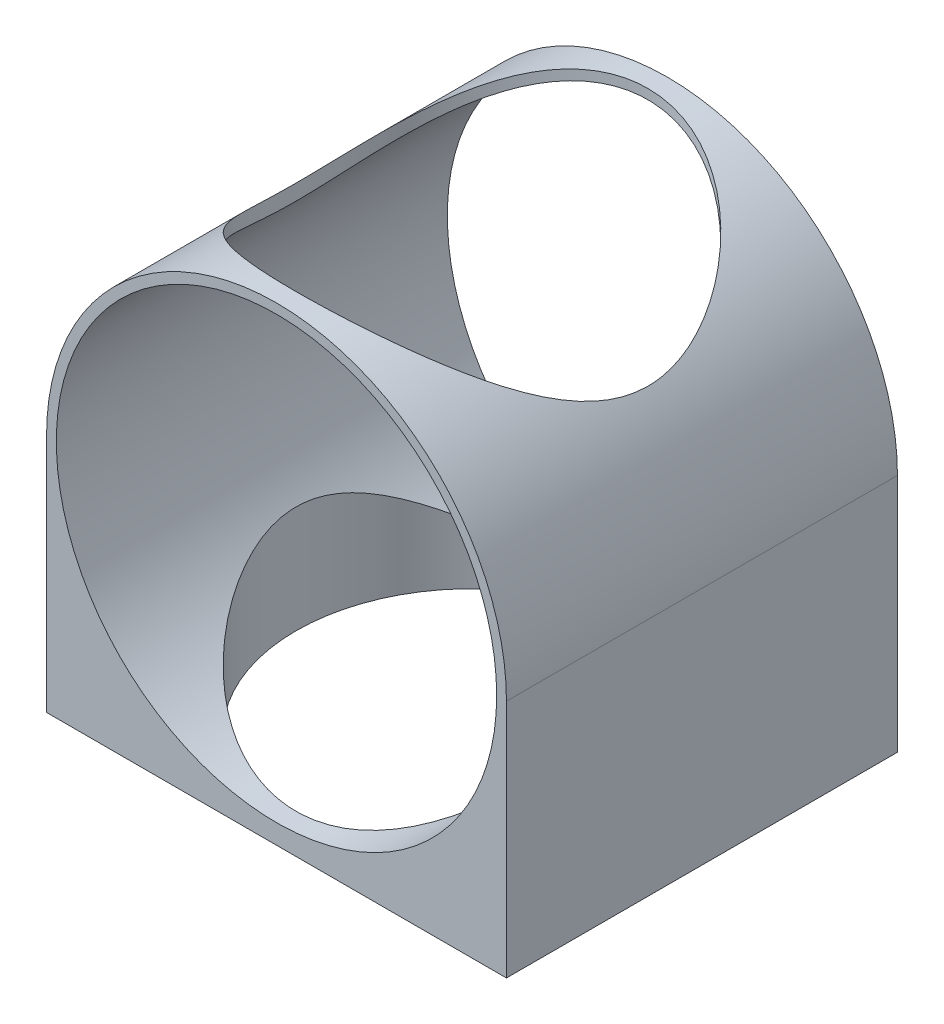
SolidWorks part; units mm, degrees
ref_plane "Front Plane" through (0, 0, 0) normal (0, 0, 1) x (1, 0, 0)
ref_plane "Top Plane" through (0, 0, 0) normal (0, 1, 0) x (1, 0, 0)
ref_plane "Right Plane" through (0, 0, 0) normal (1, 0, 0) x (0, 0, -1)
sketch "Sketch1" plane through (0, 0, 0) normal (0, 0, 1) x (1, 0, 0)
  circle A0 centre (0, 0) radius 22.225 construction
  circle A1 centre (0, 0) radius 22.225 construction
  circle A2 centre (0, 0) radius 22.525
  circle A3 centre (0, 0) radius 23.525
  dimension "D1" = 0.3
  dimension "D2" = 1.3
ref_plane "Plane1" through (0, 0, -352.4535) normal (0, 0, 1) x (1, 0, 0)
extrude "Boss-Extrude1" add sketch "Sketch1" along normal mid plane 40 from surface at -352.4535 starting at plane "Plane1"
sketch "Sketch4" plane through (0, 0, -332.4535) normal (0, 0, 1) x (1, 0, 0)
  line L0 (23.525, 0) -> (23.525, -23.525)
  line L1 (23.525, -23.525) -> (0, -23.525)
  line L2 (0, -23.525) -> (-23.525, -23.525)
  line L3 (-23.525, -23.525) -> (-23.525, 0)
  line L5 (-23.525, -23.525) -> (23.525, -23.525)
  line L6 (-23.525, -23.525) -> (-23.525, -24.525)
  line L7 (-23.525, -24.525) -> (23.525, -24.525)
  line L8 (23.525, -23.525) -> (23.525, -24.525)
  circle A0 centre (0, 0) radius 23.525 construction
  circle M6 centre (0, 0) radius 23.525
  dimension "D1" = 1
extrude "Boss-Extrude2" add sketch "Sketch4" against normal blind 40 contours L8 L1 L2 L6 L7 | L3 L2 M6 | L1 L0 M6
sketch "Sketch3" plane through (0, -50, 0) normal (0, -1, 0) x (1, 0, 0)
  circle A0 centre (0, -352.4535) radius 18 construction
  circle A1 centre (0, -352.4535) radius 18
extrude "Cut-Extrude1" cut sketch "Sketch3" against normal through all
